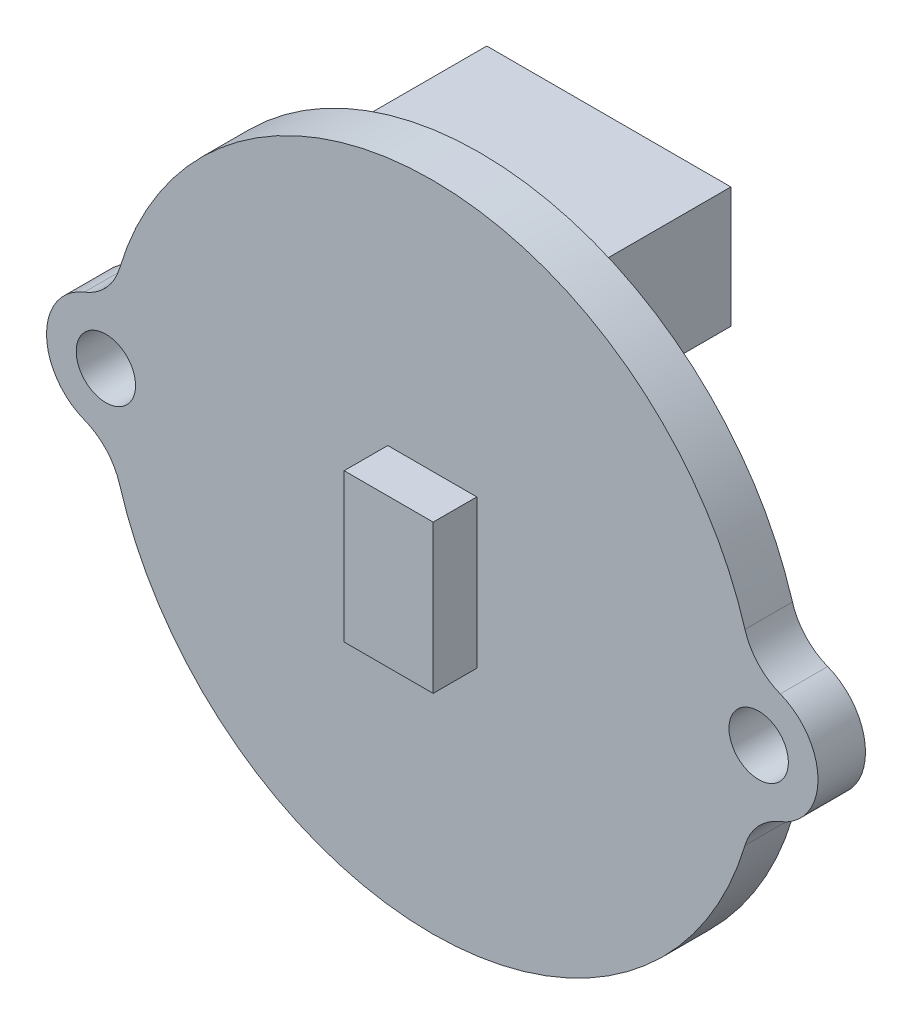
SolidWorks part; units mm, degrees
ref_plane "前视基准面" through (0, 0, 0) normal (0, 0, 1) x (1, 0, 0)
ref_plane "上视基准面" through (0, 0, 0) normal (0, 1, 0) x (1, 0, 0)
ref_plane "右视基准面" through (0, 0, 0) normal (1, 0, 0) x (0, 0, -1)
sketch "草图1" plane through (0, 0, 0) normal (0, 0, 1) x (1, 0, 0)
  line L0 (-25.0558, 0) -> (26.8683, 0) construction
  line L1 (0, 14.4071) -> (0, -14.647) construction
  arc A0 (-10.5385, -3.1529) -> (10.5385, -3.1529) centre (0, 0) ccw
  arc A1 (-11.7273, 1.8631) -> (-11.7273, -1.8631) centre (-11, 0) ccw
  arc A2 (11.7273, 1.8631) -> (11.7273, -1.8631) centre (11, 0) cw
  arc A3 (10.5385, 3.1529) -> (-10.5385, 3.1529) centre (0, 0) ccw
  arc A4 (10.5385, 3.1529) -> (11.7273, 1.8631) centre (12.4545, 3.7262) ccw
  arc A5 (10.5385, -3.1529) -> (11.7273, -1.8631) centre (12.4545, -3.7262) cw
  arc A6 (-10.5385, -3.1529) -> (-11.7273, -1.8631) centre (-12.4545, -3.7262) ccw
  arc A7 (-11.7273, 1.8631) -> (-10.5385, 3.1529) centre (-12.4545, 3.7262) ccw
  circle A8 centre (-11, 0) radius 1
  circle A9 centre (11, 0) radius 1
  dimension "D1" = 22
  dimension "D2" = 4
  dimension "D3" = 2
  dimension "D4" = 2
  dimension "D5" = 22
extrude "凸台-拉伸1" add sketch "草图1" along normal blind 1.6
sketch "草图2" plane through (0, 0, 1.6) normal (0, 0, 1) x (1, 0, 0)
  line L0 (-24.4339, 0) -> (26.5272, 0) construction
  line L1 (0, 17.5224) -> (0, -18.6412) construction
  line L3 (1.5, -2.5) -> (-1.5, -2.5)
  line L4 (1.5, -2.5) -> (1.5, 2.5)
  line L5 (1.5, 2.5) -> (-1.5, 2.5)
  line L6 (-1.5, -2.5) -> (-1.5, 2.5)
  line L7 (1.5, -2.5) -> (-1.5, 2.5) construction
  line L8 (1.5, 2.5) -> (-1.5, -2.5) construction
  point P5 (0, 0)
  dimension "D1" = 3
  dimension "D2" = 5
extrude "凸台-拉伸2" add sketch "草图2" along normal blind 1.47
sketch "草图3" plane through (0, 0, 0) normal (0, 0, -1) x (-1, 0, 0)
  line L0 (-16.9805, 0) -> (19.1318, 0) construction
  line L1 (0, 14.6922) -> (0, -14.3012) construction
  line L3 (4.113, 9.879) -> (-4.113, 9.879)
  line L4 (4.113, 9.879) -> (4.113, 5.81)
  line L5 (4.113, 5.81) -> (-4.113, 5.81)
  line L6 (-4.113, 9.879) -> (-4.113, 5.81)
  line L7 (4.113, 9.879) -> (-4.113, 5.81) construction
  line L8 (4.113, 5.81) -> (-4.113, 9.879) construction
  point P5 (0, 7.8445)
  dimension "D1" = 5.81
  dimension "D2" = 4.069
  dimension "D3" = 8.226
extrude "凸台-拉伸3" add sketch "草图3" along normal blind 4.35
